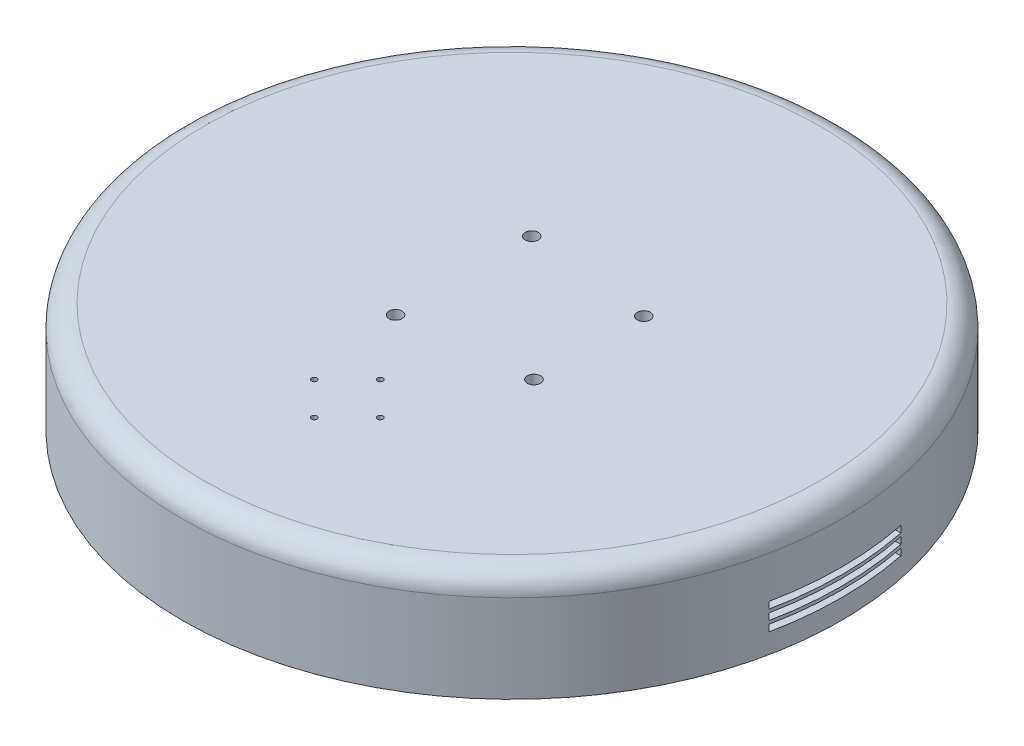
SolidWorks part; units mm, degrees
ref_plane "Front Plane" through (0, 0, 0) normal (0, 0, 1) x (1, 0, 0)
ref_plane "Top Plane" through (0, 0, 0) normal (0, 1, 0) x (1, 0, 0)
ref_plane "Right Plane" through (0, 0, 0) normal (1, 0, 0) x (0, 0, -1)
sketch "Sketch1" plane through (0, 0, 0) normal (0, 1, 0) x (1, 0, 0)
  circle A0 centre (0, 0) radius 150
  dimension "D1" = 300
extrude "Boss-Extrude1" add sketch "Sketch1" along normal blind 50
shell "Shell2" thickness 5
fillet "Fillet1" radius 10 2 edges at (0, 45, 145) (0, 50, 150)
sketch "Sketch4" plane through (0, 50, 0) normal (0, 1, 0) x (1, 0, 0)
  line L0 (0, -29.8594) -> (0, -148.7321) construction
  line L1 (-39.111, -75) -> (44.4363, -75) construction
  circle A0 centre (-22, 31) radius 3
  circle A1 centre (35, 25) radius 3
  circle A2 centre (-22, -31) radius 3
  circle A3 centre (35, -25) radius 3
  circle A4 centre (0, -60) radius 1.25
  circle A5 centre (-15, -75) radius 1.25
  circle A6 centre (0, -90) radius 1.25
  circle A7 centre (15, -75) radius 1.25
  point P0 (0, 0)
  point P22 (0, -75)
  dimension "D1" = 6
  dimension "D4" = 2.5
  dimension "D2" = 15
  dimension "D3" = 15
  dimension "D5" = 75
extrude "Cut-Extrude2" cut sketch "Sketch4" against normal through all both and the other way through all
sketch "Sketch5" plane through (0, 0, 0) normal (1, 0, 0) x (0, 0, -1)
  line L0 (-150, 0) -> (150, 0) construction
  line L1 (-30, 13.5) -> (30, 13.5)
  line L2 (-30, 13.5) -> (-30, 16.5)
  line L3 (-30, 16.5) -> (30, 16.5)
  line L4 (30, 13.5) -> (30, 16.5)
  line L5 (-30, 13.5) -> (30, 16.5) construction
  line L6 (-30, 16.5) -> (30, 13.5) construction
  line L7 (-30, 9) -> (30, 9)
  line L8 (-30, 21) -> (30, 21)
  line L9 (-30, 21) -> (-30, 18)
  line L10 (-30, 18) -> (30, 18)
  line L11 (30, 21) -> (30, 18)
  line L12 (-30, 21) -> (30, 18) construction
  line L13 (-30, 18) -> (30, 21) construction
  line L14 (-30, 9) -> (-30, 12)
  line L15 (-30, 12) -> (30, 12)
  line L16 (30, 9) -> (30, 12)
  line L17 (-30, 9) -> (30, 12) construction
  line L18 (-30, 12) -> (30, 9) construction
  point P0 (0, 15)
  point P5 (0, 10.5)
  point P10 (0, 19.5)
  dimension "D1" = 60
  dimension "D2" = 3
  dimension "D3" = 15
  dimension "D4" = 3
  dimension "D5" = 3
  dimension "D6" = 60
  dimension "D7" = 3
  dimension "D8" = 1.5
extrude "Cut-Extrude3" cut sketch "Sketch5" against normal through all both and the other way through all
